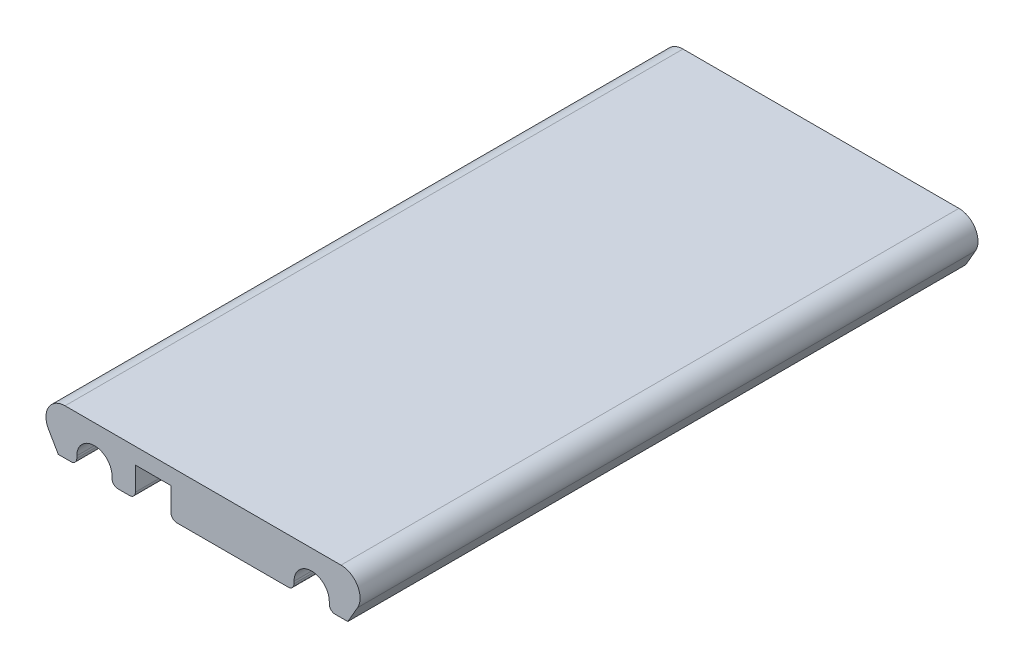
SolidWorks part; units mm, degrees
ref_plane "Front plane" through (0, 0, 0) normal (0, 0, 1) x (1, 0, 0)
ref_plane "Top plane" through (0, 0, 0) normal (0, 1, 0) x (1, 0, 0)
ref_plane "Right Plane" through (0, 0, 0) normal (1, 0, 0) x (0, 0, -1)
sketch "Sketch1" plane through (0, 0, 0) normal (0, 0, 1) x (1, 0, 0)
  line L0 (0, 0) -> (-3.3198, 5.75)
  line L1 (2.3094, 15.5) -> (96.3094, 15.5)
  line L2 (101.9386, 5.75) -> (98.6188, 0)
  line L3 (98.6188, 0) -> (92.3094, 0)
  line L4 (6.3094, 0) -> (6.3094, 2.75)
  line L5 (18.3094, 2.75) -> (18.3094, 0)
  line L6 (92.3094, 0) -> (92.3094, 2.75)
  line L8 (26.2594, 0) -> (26.2594, 10)
  line L9 (26.2594, 10) -> (38.3594, 10)
  line L10 (38.3594, 0) -> (38.3594, 10)
  line L11 (80.3094, 2.75) -> (80.3094, 0)
  line L12 (26.2594, 0) -> (18.3094, 0)
  line L13 (6.3094, 0) -> (0, 0)
  line L14 (80.3094, 0) -> (38.3594, 0)
  arc A0 (-3.3198, 5.75) -> (2.3094, 15.5) centre (2.3094, 9) cw
  arc A1 (96.3094, 15.5) -> (101.9386, 5.75) centre (96.3094, 9) cw
  arc A2 (6.3094, 2.75) -> (18.3094, 2.75) centre (12.3094, 2.75) cw
  arc A3 (92.3094, 2.75) -> (80.3094, 2.75) centre (86.3094, 2.75) ccw
  point P24 (32.3094, 10)
  dimension "D6" = 6
  dimension "D9" = 6.5
  dimension "D1" = 74
  dimension "D2" = 12.1
  dimension "D3" = 10
  dimension "D4" = 7.25
  dimension "D5" = 20
  dimension "D7" = 60
  dimension "D8" = 10
  dimension "D10" = 15.5
extrude "Boss-Extrude1" add sketch "Sketch1" along normal blind 210.5
fillet "Fillet1" radius 2 6 edges at (92.3094, 0, 105.25) (80.3094, 0, 105.25) (38.3594, 0, 105.25) (26.2594, 0, 105.25) (18.3094, 0, 105.25) (6.3094, 0, 105.25)
